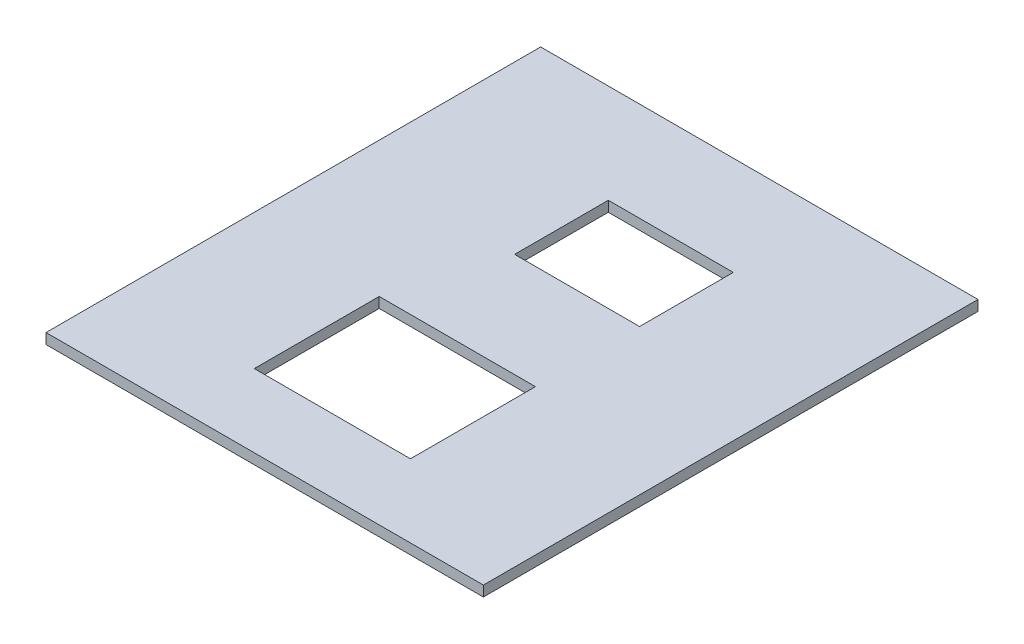
SolidWorks part; units mm, degrees
ref_plane "Front Plane" through (0, 0, 0) normal (0, 0, 1) x (1, 0, 0)
ref_plane "Top Plane" through (0, 0, 0) normal (0, 1, 0) x (1, 0, 0)
ref_plane "Right Plane" through (0, 0, 0) normal (1, 0, 0) x (0, 0, -1)
sketch "Sketch1" plane through (0, 0, 0) normal (0, 1, 0) x (1, 0, 0)
  line L1 (-21, -23.75) -> (21, -23.75)
  line L2 (-21, -23.75) -> (-21, 23.75)
  line L3 (-21, 23.75) -> (21, 23.75)
  line L4 (21, -23.75) -> (21, 23.75)
  line L5 (-21, -23.75) -> (21, 23.75) construction
  line L6 (-21, 23.75) -> (21, -23.75) construction
  point P0 (0, 0)
  dimension "D1" = 42
  dimension "D2" = 47.5
extrude "Boss-Extrude1" add sketch "Sketch1" along normal blind 1
sketch "Sketch2" plane through (0, 0, 0) normal (0, 1, 0) x (1, 0, 0)
  line L0 (1.0094, 23.75) -> (40.692, 23.75) construction
  line L2 (0, -23.75) -> (35.4556, -23.75) construction
  line L4 (21, -1.104) -> (21, -26.8441) construction
  line L6 (-21, -12.2707) -> (-21, -27.4119) construction
  line L8 (-35.4556, 14.25) -> (41.7645, 14.25) construction
  line L9 (-43.0893, 5.25) -> (43.0262, 5.25) construction
  line L10 (35.2664, -4.75) -> (-45.8652, -4.75) construction
  line L11 (-36.2758, -16.75) -> (40.3765, -16.75) construction
  line L12 (7, 41.8079) -> (7, -38.5374) construction
  line L13 (-5, 40.2817) -> (-5, -36.4661) construction
  line L14 (-8, 35.2669) -> (-8, -45.4054) construction
  line L16 (-8, -16.75) -> (7, -16.75)
  line L17 (-8, -16.75) -> (-8, -4.75)
  line L18 (-8, -4.75) -> (7, -4.75)
  line L19 (7, -16.75) -> (7, -4.75)
  line L20 (-5, 5.25) -> (7, 5.25)
  line L21 (-5, 5.25) -> (-5, 14.25)
  line L22 (-5, 14.25) -> (7, 14.25)
  line L23 (7, 5.25) -> (7, 14.25)
  point P17 (-5, 5.25)
  point P23 (7, -4.75)
  point P24 (7, -16.75)
  point P25 (-8, -16.75)
  point P26 (-8, -4.75)
  point P27 (7, 14.25)
  point P28 (7, 5.25)
  point P29 (-5, 14.25)
  dimension "D1" = 7
  dimension "D2" = 19
  dimension "D3" = 29
  dimension "D4" = 38
  dimension "D5" = 14
  dimension "D6" = 26
  dimension "D7" = 29
extrude "Cut-Extrude3" cut sketch "Sketch2" along normal blind 25
